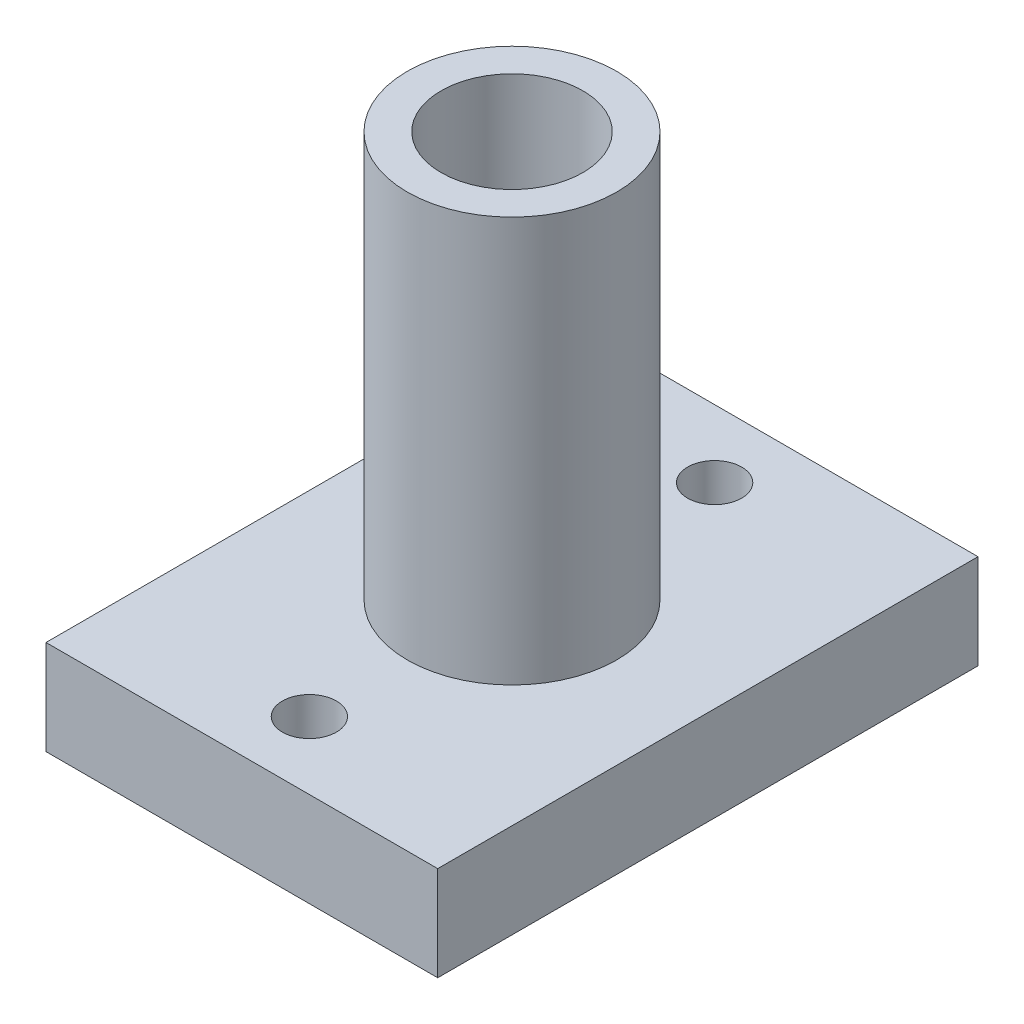
SolidWorks part; units mm, degrees
ref_plane "Front" through (0, 0, 0) normal (0, 0, 1) x (1, 0, 0)
ref_plane "Top" through (0, 0, 0) normal (0, 1, 0) x (1, 0, 0)
ref_plane "Right" through (0, 0, 0) normal (1, 0, 0) x (0, 0, -1)
sketch "Sketch1" plane through (0, 0, 0) normal (0, 0, 1) x (1, 0, 0)
  line L1 (-14.5, 3.5) -> (14.5, 3.5)
  line L2 (-14.5, 3.5) -> (-14.5, -3.5)
  line L3 (-14.5, -3.5) -> (14.5, -3.5)
  line L4 (14.5, 3.5) -> (14.5, -3.5)
  line L5 (-14.5, 3.5) -> (14.5, -3.5) construction
  line L6 (-14.5, -3.5) -> (14.5, 3.5) construction
  point P0 (0, 0)
  dimension "D1" = 7
  dimension "D2" = 29
extrude "Boss-Extrude1" add sketch "Sketch1" along normal mid plane 40
sketch "Sketch2" plane through (0, 3.5, 0) normal (0, 1, 0) x (1, 0, 0)
  line L0 (0, 0) -> (14.5, 0) construction
  line L1 (14.5, -20) -> (14.5, 20) construction
  circle A0 centre (0, 15) radius 2
  circle A2 centre (0, -15) radius 2
  dimension "D1" = 4
  dimension "D2" = 15
extrude "Cut-Extrude1" cut sketch "Sketch2" against normal through all
sketch "Sketch3" plane through (0, 3.5, 0) normal (0, 1, 0) x (1, 0, 0)
  circle A0 centre (0, 0) radius 5.25
  dimension "D1" = 10.5
extrude "Extrude-Thin1" add sketch "Sketch3" along normal blind 30 thin
